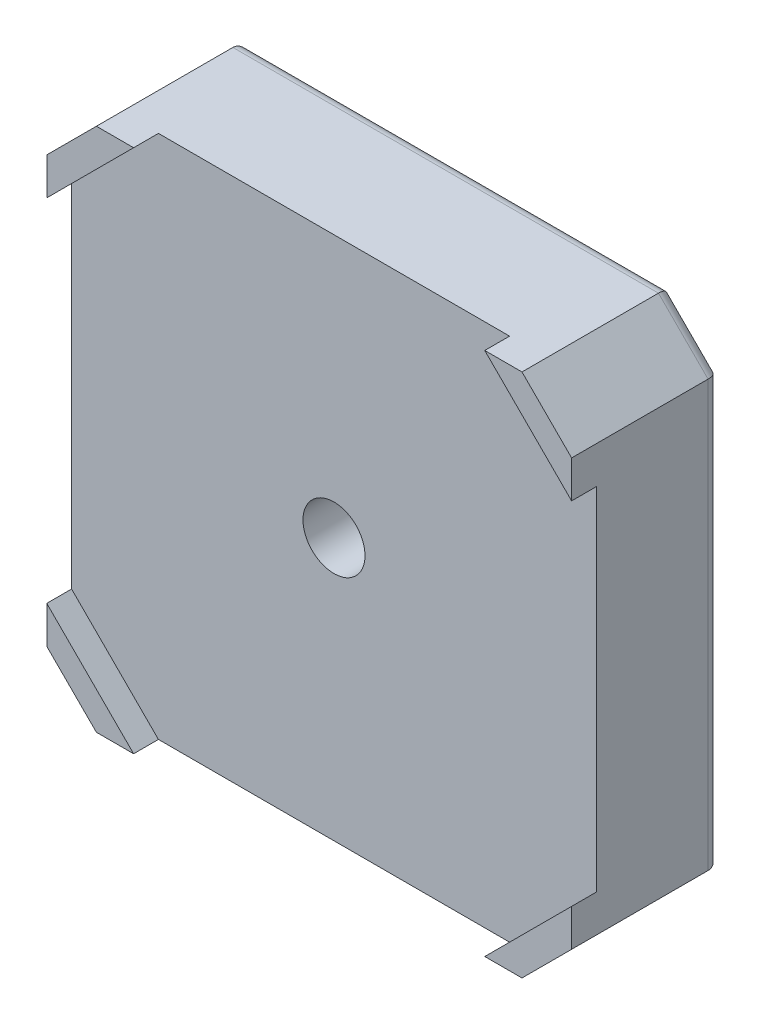
SolidWorks part; units mm, degrees
ref_plane "Front Plane" through (0, 0, 0) normal (0, 0, 1) x (1, 0, 0)
ref_plane "Top Plane" through (0, 0, 0) normal (0, 1, 0) x (1, 0, 0)
ref_plane "Right Plane" through (0, 0, 0) normal (1, 0, 0) x (0, 0, -1)
sketch "Sketch1" plane through (0, 0, 0) normal (0, 0, 1) x (1, 0, 0)
  line L0 (-21.15, 17.15) -> (-17.15, 21.15)
  line L1 (-17.15, -21.15) -> (17.15, -21.15)
  line L2 (-21.15, -17.15) -> (-21.15, 17.15)
  line L3 (-17.15, 21.15) -> (17.15, 21.15)
  line L4 (21.15, -17.15) -> (21.15, 17.15)
  line L5 (-21.15, -21.15) -> (21.15, 21.15) construction
  line L6 (-21.15, 21.15) -> (21.15, -21.15) construction
  line L7 (17.15, 21.15) -> (21.15, 17.15)
  line L8 (17.15, -21.15) -> (21.15, -17.15)
  line L9 (-21.15, -17.15) -> (-17.15, -21.15)
  point P0 (0, 0)
  dimension "D1" = 42.3
  dimension "D2" = 42.3
extrude "Boss-Extrude1" add sketch "Sketch1" along normal blind 12
sketch "Sketch2" plane through (0, 0, 12) normal (0, 0, 1) x (1, 0, 0)
  line L0 (17.15, 21.15) -> (-17.15, 21.15) construction
  line L1 (-14.15, 21.15) -> (14.15, 21.15)
  line L2 (-21.15, 14.15) -> (-21.15, -14.15)
  line L3 (-14.15, -21.15) -> (14.15, -21.15)
  line L4 (21.15, 14.15) -> (21.15, -14.15)
  line L5 (-21.15, 21.15) -> (21.15, -21.15) construction
  line L6 (-21.15, -21.15) -> (21.15, 21.15) construction
  line L7 (-21.15, 17.15) -> (-21.15, -17.15) construction
  line L8 (-21.15, 14.15) -> (-14.15, 21.15)
  line L9 (14.15, 21.15) -> (21.15, 14.15)
  line L10 (14.15, -21.15) -> (21.15, -14.15)
  line L11 (-21.15, -14.15) -> (-14.15, -21.15)
  point P0 (0, 0)
extrude "Cut-Extrude1" cut sketch "Sketch2" against normal blind 2
sketch "Sketch3" plane through (0, 0, 0) normal (0, 0, -1) x (-1, 0, 0)
  circle A0 centre (0, 0) radius 11
  dimension "D1" = 22
extrude "Boss-Extrude2" add sketch "Sketch3" along normal blind 2
sketch "Sketch4" plane through (0, 0, -2) normal (0, 0, -1) x (-1, 0, 0)
  circle A0 centre (0, 0) radius 5.5
  dimension "D1" = 11
extrude "Cut-Extrude2" cut sketch "Sketch4" against normal blind 7
sketch "Sketch5" plane through (0, 0, 5) normal (0, 0, -1) x (-1, 0, 0)
  circle A0 centre (0, 0) radius 2.5
  dimension "D1" = 5
extrude "Cut-Extrude3" cut sketch "Sketch5" against normal through all
fillet "Fillet1" radius 1 8 edges at (19.15, 19.15, 0) (21.15, 0, 0) (19.15, -19.15, 0) (0, -21.15, 0) (-19.15, -19.15, 0) (-21.15, 0, 0) (-19.15, 19.15, 0) (0, 21.15, 0)
fillet "Fillet2" radius 0.5 3 edges at (-5.5, 0, -2) (-5.5, 0, 5) (-11, 0, -2)
sketch "Sketch6" plane through (0, 0, 0) normal (0, 0, -1) x (-1, 0, 0)
  line L1 (-15.5, 15.5) -> (15.5, 15.5) construction
  line L2 (-15.5, 15.5) -> (-15.5, -15.5) construction
  line L3 (-15.5, -15.5) -> (15.5, -15.5) construction
  line L4 (15.5, 15.5) -> (15.5, -15.5) construction
  line L5 (-15.5, 15.5) -> (15.5, -15.5) construction
  line L6 (-15.5, -15.5) -> (15.5, 15.5) construction
  circle A0 centre (-15.5, 15.5) radius 1.5
  circle A1 centre (-15.5, -15.5) radius 1.5
  circle A2 centre (15.5, -15.5) radius 1.5
  circle A3 centre (15.5, 15.5) radius 1.5
  point P0 (0, 0)
  dimension "D2" = 3
  dimension "D1" = 31
extrude "Cut-Extrude4" cut sketch "Sketch6" against normal blind 3
fillet "Fillet3" radius 0.5 4 edges at (14, -15.5, 0) (-14, -15.5, 0) (-14, 15.5, 0) (14, 15.5, 0)
